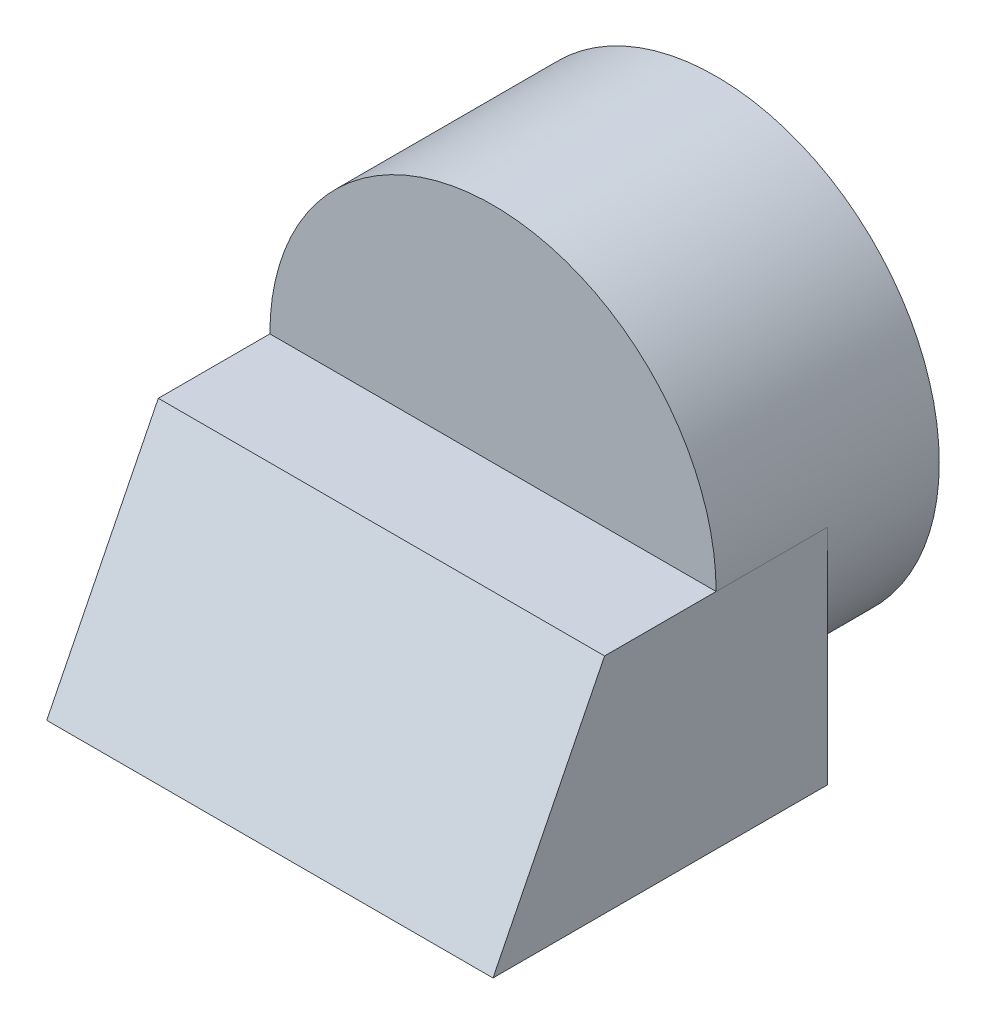
SolidWorks part; units mm, degrees
ref_plane "Front" through (0, 0, 0) normal (0, 0, 1) x (1, 0, 0)
ref_plane "Top" through (0, 0, 0) normal (0, 1, 0) x (1, 0, 0)
ref_plane "Right" through (0, 0, 0) normal (1, 0, 0) x (0, 0, -1)
sketch "Sketch1" plane through (0, 0, 0) normal (0, 1, 0) x (1, 0, 0)
  line L1 (-2, -2) -> (2, -2)
  line L2 (-2, -2) -> (-2, 2)
  line L3 (-2, 2) -> (2, 2)
  line L4 (2, -2) -> (2, 2)
  line L5 (-2, -2) -> (2, 2) construction
  line L6 (-2, 2) -> (2, -2) construction
  point P0 (0, 0)
  dimension "D1" = 4
  dimension "D2" = 4
extrude "Boss-Extrude1" add sketch "Sketch1" along normal blind 4
sketch "Sketch2" plane through (0, 0, 2) normal (0, 0, 1) x (1, 0, 0)
  line L0 (-2, 4) -> (-2, 0) construction
  line L1 (2, 4) -> (2, 0) construction
  line L2 (-2, 2) -> (-2, 4)
  line L3 (-2, 4) -> (2, 4)
  line L4 (2, 4) -> (2, 2)
  arc A0 (-2, 2) -> (2, 2) centre (0, 2) cw
  line M2 (2, 0) -> (2, 4)
  line M3 (2, 4) -> (-2, 4)
  line M4 (-2, 4) -> (-2, 0)
extrude "Cut-Extrude1" cut sketch "Sketch2" against normal blind 4 contours A0 L3 M4 | A0 M3 M2
sketch "Sketch3" plane through (-2, 0, 0) normal (-1, 0, 0) x (0, 0, 1)
  line L0 (2, 0) -> (1, 2)
  line L1 (-2, 2) -> (2, 2) construction
  line L2 (1, 2) -> (0, 2)
  line L3 (0, 2) -> (0, 4)
  line L4 (2, 4) -> (-2, 4) construction
  line L5 (0, 4) -> (2, 4)
  line L6 (2, 2) -> (2, 4) construction
  line L7 (2, 4) -> (2, 0)
  dimension "D1" = 2
  dimension "D2" = 1
extrude "Cut-Extrude2" cut sketch "Sketch3" against normal blind 4
sketch "Sketch4" plane through (0, 0, -2) normal (0, 0, -1) x (-1, 0, 0)
  line L0 (-2, 2) -> (-2, 0)
  line L1 (-2, 0) -> (2, 0)
  line L2 (2, 0) -> (2, 2)
  arc A0 (-2, 2) -> (2, 2) centre (0, 2) ccw
  line M2 (-2, 2) -> (-2, 0)
  line M3 (-2, 0) -> (2, 0)
  line M4 (2, 0) -> (2, 2)
extrude "Cut-Extrude3" cut sketch "Sketch4" against normal blind 1 contours A0 M2 M3 | A0 L1 M4
